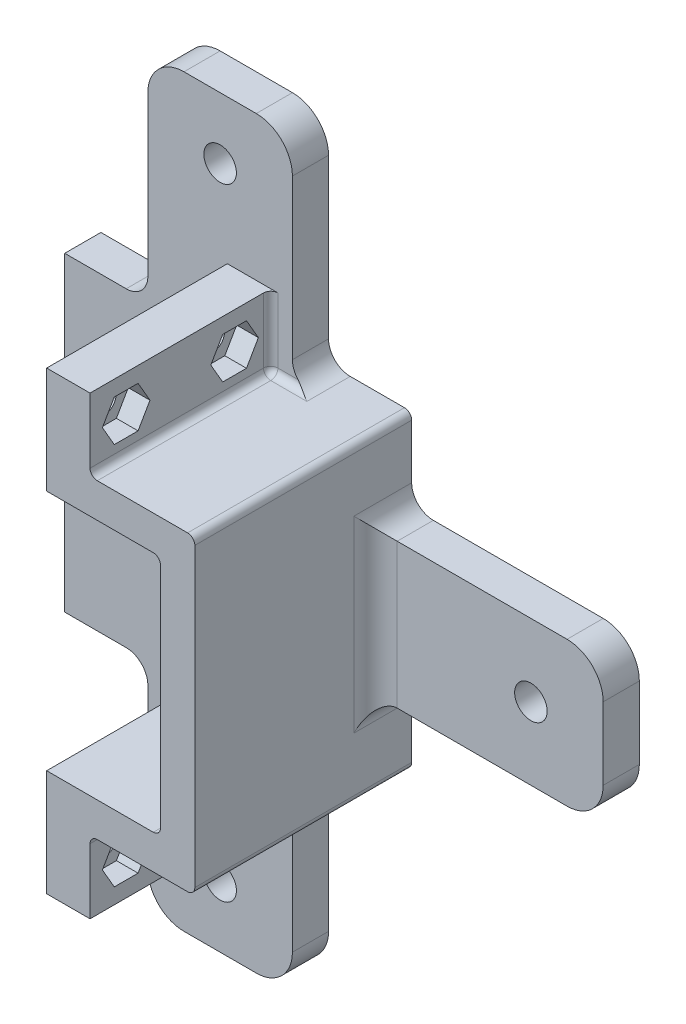
SolidWorks part; units mm, degrees
material "PBT General Purpose"
ref_plane "Front Plane" through (0, 0, 0) normal (0, 0, 1) x (1, 0, 0)
ref_plane "Top Plane" through (0, 0, 0) normal (0, 1, 0) x (1, 0, 0)
ref_plane "Right Plane" through (0, 0, 0) normal (1, 0, 0) x (0, 0, -1)
sketch "Sketch1" plane through (0, 0, 0) normal (0, 0, 1) x (1, 0, 0)
  line L0 (0, 0) -> (33, 0)
  line L1 (0, 0) -> (0, 33)
  line L2 (33, 0) -> (33, 33)
  line L3 (0, 33) -> (33, 33)
  line L4 (-5, 38) -> (38, 38)
  line L5 (-5, 38) -> (-5, -5)
  line L6 (38, 38) -> (38, -5)
  line L7 (-5, -5) -> (38, -5)
  dimension "D1" = 33
  dimension "D2" = 33
  dimension "D3" = 5
  dimension "D4" = 5
  dimension "D5" = 5
  dimension "D6" = 5
extrude "Boss-Extrude1" add sketch "Sketch1" along normal blind 25
sketch "Sketch3" plane through (0, 0, 0) normal (0, 0, -1) x (-1, 0, 0)
  line L0 (-38, 38) -> (5, 38) construction
  line L1 (-38, -5) -> (-38, 38) construction
  line L2 (5, 38) -> (5, -5) construction
  line L3 (5, -5) -> (-38, -5) construction
  line L4 (-38, 38) -> (5, 38)
  line L5 (-38, -5) -> (-38, 38)
  line L6 (5, 38) -> (5, -5)
  line L7 (5, -5) -> (-38, -5)
extrude "Boss-Extrude2" add sketch "Sketch3" along normal blind 5
sketch "Sketch4" plane through (0, 38, 0) normal (0, 1, 0) x (1, 0, 0)
  line L0 (26.5, 0) -> (26.5, 5)
  line L1 (26.5, 0) -> (6.5, 0)
  line L2 (26.5, 5) -> (6.5, 5)
  line L3 (6.5, 0) -> (6.5, 5)
  line L4 (-5, 5) -> (38, 5) construction
  line L5 (16.5, -25) -> (16.5, 5) construction
  line L6 (38, -25) -> (-5, -25) construction
  line L7 (16.5, 0) -> (16.5, 5) construction
  dimension "D1" = 5
  dimension "D2" = 20
extrude "Boss-Extrude3" add sketch "Sketch4" along normal blind 30
sketch "Sketch5" plane through (0, 0, 0) normal (0, 0, 1) x (1, 0, 0)
  line L0 (16.5, 68) -> (16.5, 38) construction
  line L1 (6.5, 68) -> (26.5, 68) construction
  line L2 (6.5, 38) -> (26.5, 38) construction
  circle A0 centre (16.5, 59.5) radius 2.25
  dimension "D1" = 8.5
  dimension "D2" = 4.5
extrude "Cut-Extrude1" cut sketch "Sketch5" against normal through all
sketch "Sketch6" plane through (0, 0, 25) normal (0, 0, 1) x (1, 0, 0)
  line L0 (-5, 16.5) -> (38, 16.5) construction
  line L1 (-5, 38) -> (-5, -5) construction
  line L2 (38, -5) -> (38, 38) construction
ref_plane "Plane1" through (0, 16.5, 0) normal (0, -1, 0) x (1, 0, 0)
mirror "Mirror1" about plane through (0, 16.5, 0) normal (0, -1, 0) of "Cut-Extrude1", "Boss-Extrude3"
sketch "Эскиз1" plane through (0, 0, 25) normal (0, 0, 1) x (1, 0, 0)
  line L0 (16.5, 38) -> (16.5, -5)
  line L3 (16.5, 38) -> (-5, 38)
  line L4 (16.5, -5) -> (-5, -5)
  line L5 (-5, 38) -> (-5, -5)
  line L6 (38, 38) -> (-5, 38) construction
  line L7 (-5, -5) -> (38, -5) construction
  line L8 (-5, 38) -> (-5, -5) construction
extrude "Вырез-Вытянуть1" cut sketch "Эскиз1" against normal up to surface (25 mm away) up to face at (18.75, -26.5, 0)
sketch "Эскиз3" plane through (16.5, 0, 0) normal (-1, 0, 0) x (0, 0, 1)
  line L0 (25, -5) -> (0, -5)
  line L1 (25, -5) -> (25, -15)
  line L2 (0, -5) -> (0, -15)
  line L3 (25, -15) -> (0, -15)
  dimension "D1" = 10
extrude "Бобышка-Вытянуть1" add sketch "Эскиз3" against normal blind 7
fillet "Скругление1" radius 1 1 edges at (23.5, -5, 12.5)
sketch "Эскиз4" plane through (16.5, 0, 0) normal (-1, 0, 0) x (0, 0, 1)
  line L0 (25, -10) -> (0, -10) construction
  line L1 (25, -15) -> (25, 0) construction
  line L2 (0, 0) -> (0, -15) construction
  line L3 (0, -15) -> (25, -15) construction
  circle A0 centre (20, -10) radius 1.6
  circle A1 centre (5, -10) radius 1.6
  dimension "D2" = 3.2
  dimension "D3" = 3.2
  dimension "D4" = 5
  dimension "D5" = 5
  dimension "D1" = 5
extrude "Вырез-Вытянуть2" cut sketch "Эскиз4" against normal through all
sketch "Эскиз5" plane through (23.5, 0, 0) normal (1, 0, 0) x (0, 0, -1)
  line L0 (-20, -10) -> (-5, -10) construction
  line L1 (-18.3546, -12.85) -> (-16.7091, -10)
  line L2 (-16.7091, -10) -> (-18.3546, -7.15)
  line L3 (-18.3546, -7.15) -> (-21.6454, -7.15)
  line L4 (-21.6454, -7.15) -> (-23.2909, -10)
  line L5 (-23.2909, -10) -> (-21.6454, -12.85)
  line L6 (-21.6454, -12.85) -> (-18.3546, -12.85)
  line L7 (-6.6454, -12.85) -> (-3.3546, -12.85)
  line L8 (-3.3546, -12.85) -> (-1.7091, -10)
  line L9 (-1.7091, -10) -> (-3.3546, -7.15)
  line L10 (-3.3546, -7.15) -> (-6.6454, -7.15)
  line L11 (-6.6454, -7.15) -> (-8.2909, -10)
  line L12 (-8.2909, -10) -> (-6.6454, -12.85)
  circle A0 centre (-20, -10) radius 2.85 construction
  circle A1 centre (-5, -10) radius 2.85 construction
  dimension "D1" = 5.7
  dimension "D2" = 5.7
extrude "Вырез-Вытянуть3" cut sketch "Эскиз5" against normal blind 3
mirror "Зеркальное отражение2" about plane through (0, 16.5, 0) normal (0, -1, 0) of "Бобышка-Вытянуть1"
mirror "Зеркальное отражение3" about plane through (0, 16.5, 0) normal (0, -1, 0) of "Вырез-Вытянуть2"
mirror "Зеркальное отражение4" about plane through (0, 16.5, 0) normal (0, -1, 0) of "Вырез-Вытянуть3"
sketch "Эскиз6" plane through (0, 0, 25) normal (0, 0, 1) x (1, 0, 0)
  line L0 (16.5, 33.25) -> (33.25, 33.25)
  line L1 (16.5, 33.25) -> (16.5, -0.25)
  line L2 (33.25, 33.25) -> (33.25, -0.25)
  line L3 (16.5, -0.25) -> (33.25, -0.25)
  line L4 (16.5, 33) -> (16.5, 48) construction
  line L5 (33, 0) -> (33, 33) construction
  line L6 (33, 33) -> (16.5, 33) construction
  line L7 (16.5, 0) -> (33, 0) construction
  dimension "D1" = 0.25
  dimension "D2" = 0.25
  dimension "D3" = 0.25
extrude "Вырез-Вытянуть4" cut sketch "Эскиз6" against normal up to surface (25 mm away) up to face at (17.7282, 15.4384, 0)
fillet "Скругление2" radius 1 1 edges at (23.5, 38, 12.5)
fillet "Скругление3" radius 1 6 edges at (25.5, -5, 0) (23.7929, -5.2929, 0) (25.5, 38, 0) (23.7929, 38.2929, 0) (23.5, -10.5, 0) (23.5, 43.5, 0)
fillet "Скругление4" radius 5 4 edges at (6.5, -35, -2.5) (26.5, -35, -2.5) (6.5, 68, -2.5) (26.5, 68, -2.5)
fillet "Скругление6" radius 1 5 edges at (24.875, 33.25, 0) (33.25, 16.5, 0) (24.875, -0.25, 0) (33.25, -0.25, 12.5) (33.25, 33.25, 12.5)
sketch "Эскиз7" plane through (16.5, 0, 0) normal (-1, 0, 0) x (0, 0, 1)
  line L4 (0, 48) -> (0, 32.25)
  line L5 (1, 33.25) -> (25, 33.25)
  line L6 (25, 33.25) -> (25, 48)
  line L7 (25, 48) -> (0, 48)
  line L8 (0, 48) -> (0, 32.25)
  line L9 (1, 33.25) -> (25, 33.25)
  line L10 (25, 33.25) -> (25, 48)
  line L11 (25, 48) -> (0, 48)
  line L12 (25, -15) -> (25, -0.25)
  line L13 (25, -0.25) -> (1, -0.25)
  line L14 (0, 0.75) -> (0, -15)
  line L15 (0, -15) -> (25, -15)
  line L16 (25, -15) -> (25, -0.25)
  line L17 (25, -0.25) -> (1, -0.25)
  line L18 (0, 0.75) -> (0, -15)
  line L19 (0, -15) -> (25, -15)
  arc A1 (1, 33.25) -> (0, 32.25) centre (1, 32.25) ccw
  arc A2 (1, 33.25) -> (0, 32.25) centre (1, 32.25) ccw
  arc A3 (0, 0.75) -> (1, -0.25) centre (1, 0.75) ccw
  arc A4 (0, 0.75) -> (1, -0.25) centre (1, 0.75) ccw
  dimension "D1" = 0
  dimension "D2" = 0
extrude "Вырез-Вытянуть5" cut sketch "Эскиз7" against normal blind 1
sketch "Эскиз9" plane through (38, 0, 0) normal (1, 0, 0) x (0, 0, -1)
  line L0 (5, 16.5) -> (-13.0756, 16.5) construction
  line L1 (5, 38) -> (5, -5) construction
  line L2 (5, 6.5) -> (5, 26.5)
  line L3 (5, 6.5) -> (0, 6.5)
  line L4 (5, 26.5) -> (0, 26.5)
  line L5 (0, 6.5) -> (0, 26.5)
  line L6 (0, 16.5) -> (5, 16.5) construction
  dimension "D1" = 20
  dimension "D2" = 5
extrude "Бобышка-Вытянуть2" add sketch "Эскиз9" along normal blind 31.5
sketch "Эскиз10" plane through (0, 0, 0) normal (0, 0, 1) x (1, 0, 0)
  line L0 (69.5, 16.5) -> (38, 16.5) construction
  line L1 (69.5, 26.5) -> (69.5, 6.5) construction
  line L2 (38, 26.5) -> (38, 6.5) construction
  circle A0 centre (59.5, 16.5) radius 2.25
  dimension "D1" = 4.5
  dimension "D2" = 10
extrude "Вырез-Вытянуть6" cut sketch "Эскиз10" against normal through all
fillet "Скругление7" radius 5 2 edges at (69.5, 6.5, -2.5) (69.5, 26.5, -2.5)
fillet "Скругление8" radius 3 7 edges at (38, 16.5, 0)
fillet "Скругление9" radius 1 2 edges at (38, -5, 10) (38, 38, 10)
